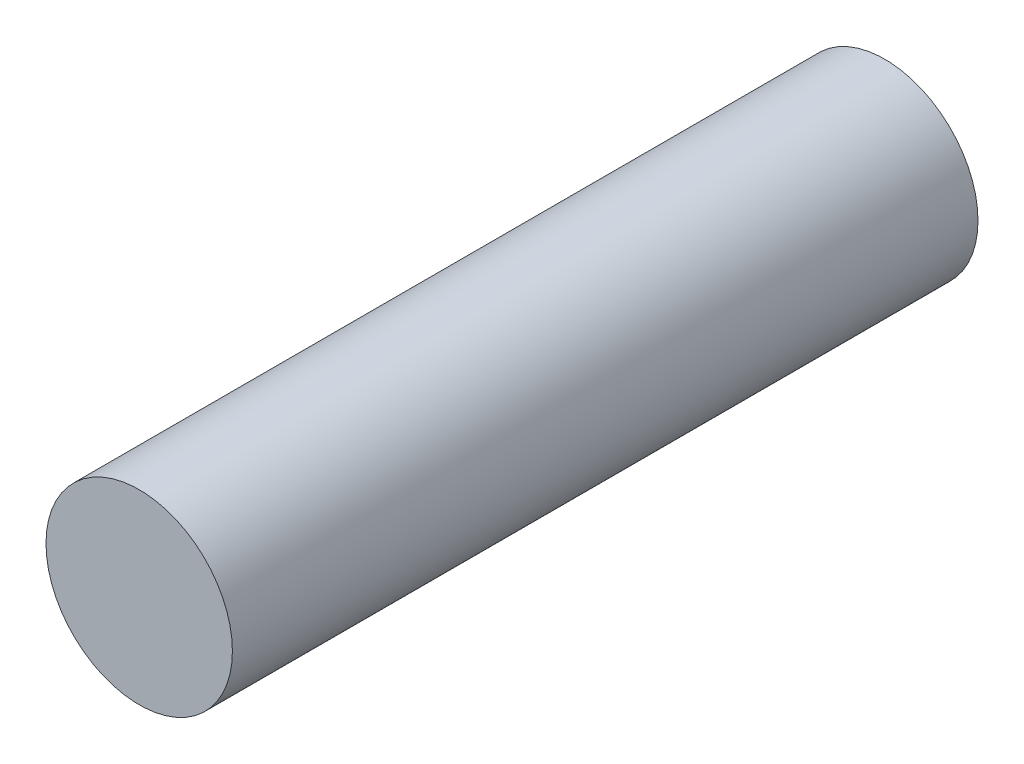
SolidWorks part; units mm, degrees
material "CA"
ref_plane "Front Plane" through (0, 0, 0) normal (0, 0, 1) x (1, 0, 0)
ref_plane "Top Plane" through (0, 0, 0) normal (0, 1, 0) x (1, 0, 0)
ref_plane "Right Plane" through (0, 0, 0) normal (1, 0, 0) x (0, 0, -1)
sketch "Sketch1" plane through (0, 0, 0) normal (0, 0, 1) x (1, 0, 0)
  circle A0 centre (0, 0) radius 6.35
  dimension "D1" = 12.7
extrude "Boss-Extrude1" add sketch "Sketch1" along normal blind 50.8
sketch "Sketch2" plane through (0, 0, 0) normal (0, 0, -1) x (-1, 0, 0)
  circle A0 centre (0, 0) radius 1.5875
  dimension "D1" = 3.175
extrude "Cut-Extrude1" cut sketch "Sketch2" against normal blind 12.7
